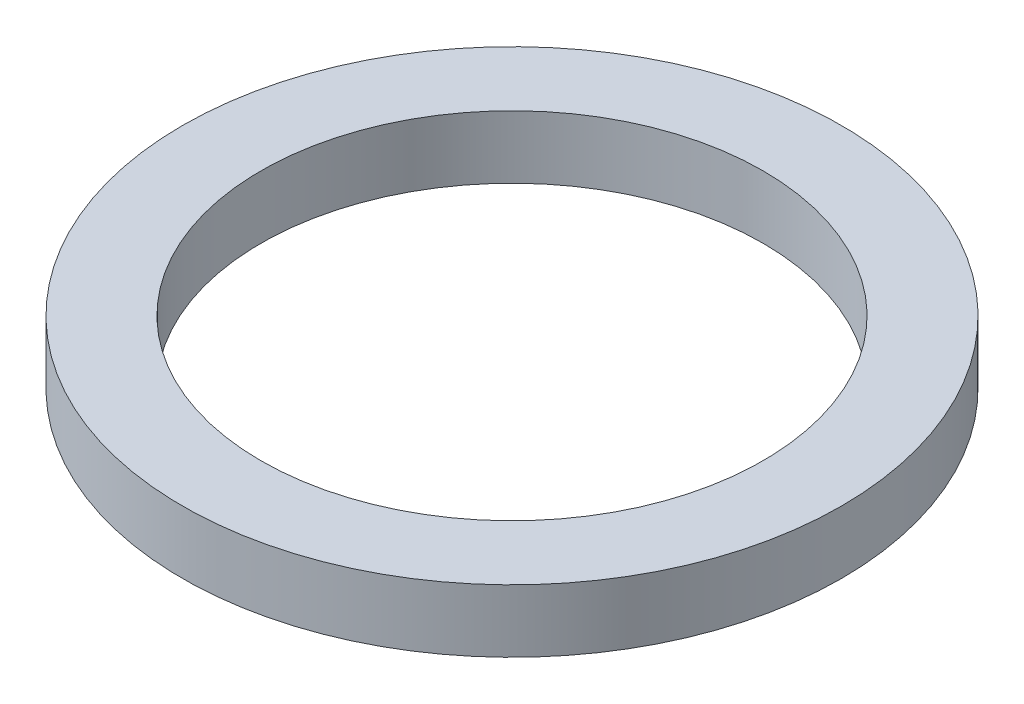
SolidWorks part; units mm, degrees
ref_plane "Front Plane" through (0, 0, 0) normal (0, 0, 1) x (1, 0, 0)
ref_plane "Top Plane" through (0, 0, 0) normal (0, 1, 0) x (1, 0, 0)
ref_plane "Right Plane" through (0, 0, 0) normal (1, 0, 0) x (0, 0, -1)
sketch "Sketch1" plane through (0, 0, 0) normal (0, 1, 0) x (1, 0, 0)
  circle A0 centre (0, 0) radius 4
  dimension "D1" = 8
extrude "Extrude-Thin1" add sketch "Sketch1" along normal blind 1 thin
